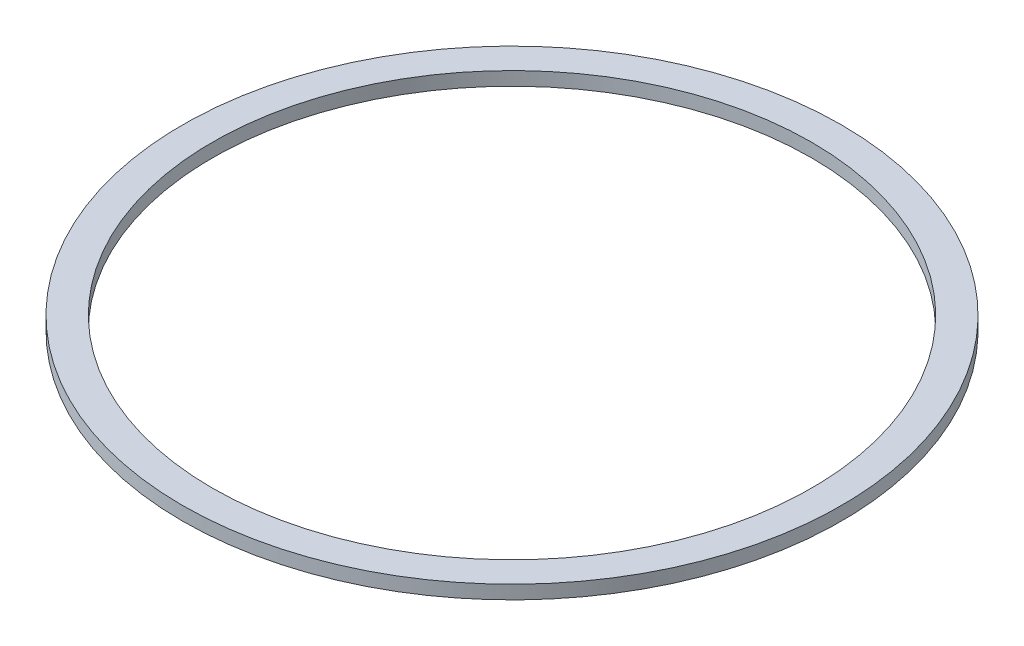
SolidWorks part; units mm, degrees
material "Cast Alloy Steel"
ref_plane "Front Plane" through (0, 0, 0) normal (0, 0, 1) x (1, 0, 0)
ref_plane "Top Plane" through (0, 0, 0) normal (0, 1, 0) x (1, 0, 0)
ref_plane "Right Plane" through (0, 0, 0) normal (1, 0, 0) x (0, 0, -1)
sketch "Sketch1" plane through (0, 0, 0) normal (0, 1, 0) x (1, 0, 0)
  circle A0 centre (0, 0) radius 38.1
  circle A1 centre (0, 0) radius 41.91
  dimension "D1" = 83.82
  dimension "D2" = 76.2
extrude "Boss-Extrude1" add sketch "Sketch1" along normal blind 1.7272
